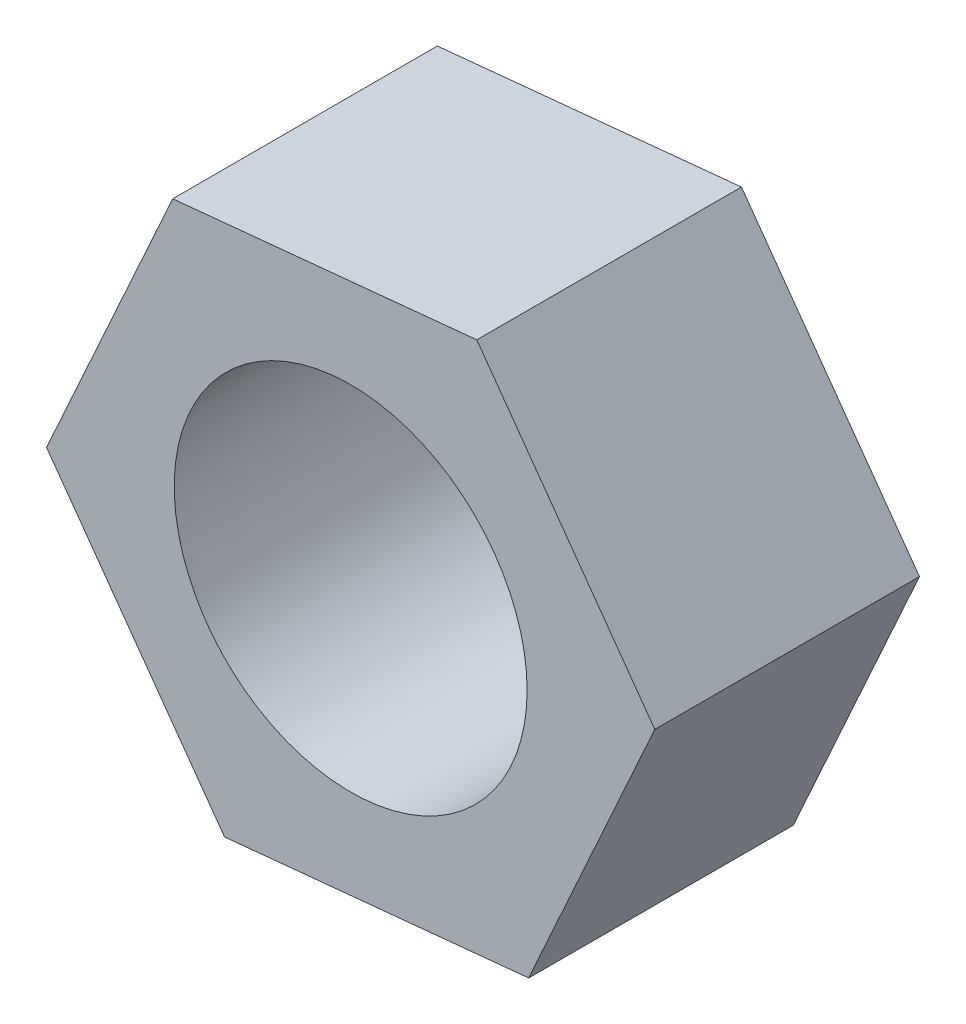
SolidWorks part; units mm, degrees
material "1.0558 (G300)"
ref_plane "Ön Düzlem" through (0, 0, 0) normal (0, 0, 1) x (1, 0, 0)
ref_plane "Üst Düzlem" through (0, 0, 0) normal (0, 1, 0) x (1, 0, 0)
ref_plane "Sağ Düzlem" through (0, 0, 0) normal (1, 0, 0) x (0, 0, -1)
sketch "Çizim1" plane through (0, 0, 0) normal (0, 0, 1) x (1, 0, 0)
  line L1 (10.0877, -14.0797) -> (17.2372, 1.6963)
  line L2 (17.2372, 1.6963) -> (7.1495, 15.7761)
  line L3 (7.1495, 15.7761) -> (-10.0877, 14.0797)
  line L4 (-10.0877, 14.0797) -> (-17.2372, -1.6963)
  line L5 (-17.2372, -1.6963) -> (-7.1495, -15.7761)
  line L6 (-7.1495, -15.7761) -> (10.0877, -14.0797)
  circle A0 centre (0, 0) radius 15 construction
  circle A1 centre (0, 0) radius 10
  dimension "D2" = 20
  dimension "D1" = 30
extrude "Yükseklik-Ekstrüzyon1" add sketch "Çizim1" along normal blind 15
